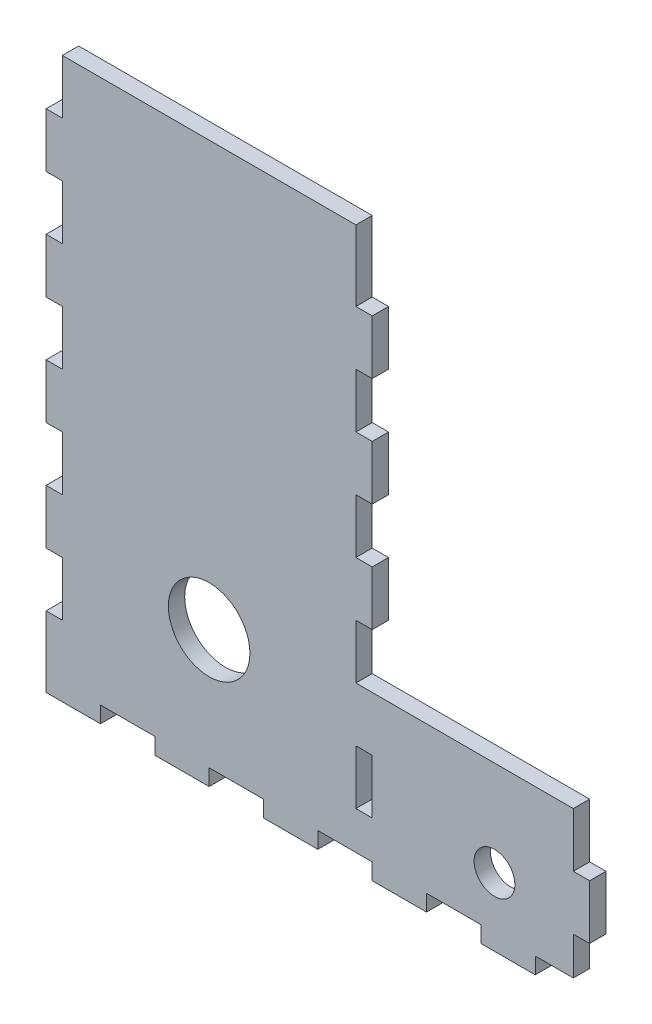
SolidWorks part; units mm, degrees
ref_plane "Front Plane" through (0, 0, 0) normal (0, 0, 1) x (1, 0, 0)
ref_plane "Top Plane" through (0, 0, 0) normal (0, 1, 0) x (1, 0, 0)
ref_plane "Right Plane" through (0, 0, 0) normal (1, 0, 0) x (0, 0, -1)
sketch "Sketch1" plane through (0, 0, 0) normal (0, 0, 1) x (1, 0, 0)
  line L1 (-17.3309, 199.4274) -> (102.6691, 199.4274)
  line L2 (-17.3309, 199.4274) -> (-17.3309, -6.5726)
  line L3 (-17.3309, -6.5726) -> (102.6691, -6.5726)
  line L4 (102.6691, 199.4274) -> (102.6691, 53.4274)
  line L5 (102.6691, -6.5726) -> (182.6691, -6.5726)
  line L7 (102.6691, 53.4274) -> (182.6691, 53.4274)
  line L8 (182.6691, -6.5726) -> (182.6691, 53.4274)
  dimension "D1" = 120
  dimension "D2" = 206
  dimension "D3" = 60
  dimension "D4" = 120
  dimension "D5" = 200
extrude "Boss-Extrude1" add sketch "Sketch1" along normal blind 6
sketch "Sketch2" plane through (0, 0, 6) normal (0, 0, 1) x (1, 0, 0)
  line L0 (-17.3309, -6.5726) -> (182.6691, -6.5726) construction
  line L1 (2.6691, -6.5726) -> (22.6691, -6.5726)
  line L2 (2.6691, -6.5726) -> (2.6691, -0.5726)
  line L3 (2.6691, -0.5726) -> (22.6691, -0.5726)
  line L4 (22.6691, -6.5726) -> (22.6691, -0.5726)
  line L5 (-17.3309, 199.4274) -> (-17.3309, -6.5726) construction
  dimension "D1" = 0
  dimension "D2" = 6
  dimension "D3" = 20
  dimension "D4" = 20
extrude "Cut-Extrude1" cut sketch "Sketch2" against normal through all
pattern_linear "LPattern1" count 5 spacing 40 along (1, 0, 0) of "Cut-Extrude1"
sketch "Sketch3" plane through (0, 0, 0) normal (0, 0, 1) x (1, 0, 0)
  line L5 (102.6691, 53.4274) -> (102.6691, 199.4274) construction
  line L6 (102.6691, 33.4274) -> (96.6691, 33.4274)
  line L7 (102.6691, 33.4274) -> (102.6691, 13.4274)
  line L8 (102.6691, 13.4274) -> (96.6691, 13.4274)
  line L9 (96.6691, 33.4274) -> (96.6691, 13.4274)
  line L10 (62.6691, -6.5726) -> (82.6691, -6.5726) construction
  dimension "D1" = 0
  dimension "D2" = 20
  dimension "D3" = 20
  dimension "D4" = 6
extrude "Cut-Extrude2" cut sketch "Sketch3" along normal through all
pattern_linear "LPattern2" count 5 spacing 40 along (0, 1, 0) of "Cut-Extrude2"
sketch "Sketch4" plane through (0, 0, 6) normal (0, 0, 1) x (1, 0, 0)
  line L1 (96.6691, 193.4274) -> (102.6691, 193.4274)
  line L2 (96.6691, 193.4274) -> (96.6691, 199.4274)
  line L3 (96.6691, 199.4274) -> (102.6691, 199.4274)
  line L4 (102.6691, 193.4274) -> (102.6691, 199.4274)
extrude "Cut-Extrude3" cut sketch "Sketch4" against normal blind 10
sketch "Sketch5" plane through (0, 0, 6) normal (0, 0, 1) x (1, 0, 0)
  line L1 (182.6691, 53.4274) -> (176.6691, 53.4274)
  line L2 (182.6691, 53.4274) -> (182.6691, 33.4274)
  line L3 (182.6691, 33.4274) -> (176.6691, 33.4274)
  line L4 (176.6691, 53.4274) -> (176.6691, 33.4274)
  dimension "D1" = 20
  dimension "D2" = 6
extrude "Cut-Extrude4" cut sketch "Sketch5" against normal blind 10
pattern_linear "LPattern3" count 2 spacing 40 along (0, -1, 0) of "Cut-Extrude4"
sketch "Sketch7" plane through (0, 0, 6) normal (0, 0, 1) x (1, 0, 0)
  line L1 (-17.3309, 199.4274) -> (-11.3309, 199.4274)
  line L2 (-17.3309, 199.4274) -> (-17.3309, 179.4274)
  line L3 (-17.3309, 179.4274) -> (-11.3309, 179.4274)
  line L4 (-11.3309, 199.4274) -> (-11.3309, 179.4274)
  dimension "D1" = 6
  dimension "D2" = 20
extrude "Cut-Extrude5" cut sketch "Sketch7" against normal blind 10
pattern_linear "LPattern4" count 5 spacing 40 along (0, -1, 0) of "Cut-Extrude5"
sketch "Sketch8" plane through (0, 0, 0) normal (0, 0, -1) x (-1, 0, 0)
  line L0 (17.3309, 59.4274) -> (17.3309, 39.4274) construction
  line L1 (-22.6691, -6.5726) -> (-42.6691, -6.5726) construction
  line L3 (-102.6691, 73.4274) -> (-102.6691, 93.4274) construction
  circle A0 centre (-42.6691, 43.4274) radius 15
  point P6 (0, 0)
  dimension "D1" = 30
  dimension "D2" = 60
  dimension "D3" = 50
  dimension "D4" = 60
extrude "Cut-Extrude6" cut sketch "Sketch8" against normal blind 10
sketch "Sketch9" plane through (0, 0, 0) normal (0, 0, -1) x (-1, 0, 0)
  line L0 (-142.6691, -6.5726) -> (-162.6691, -6.5726) construction
  line L1 (-182.6691, 13.4274) -> (-182.6691, 33.4274) construction
  circle A1 centre (-147.6691, 18.4274) radius 7.5
  dimension "D1" = 25
  dimension "D2" = 35
extrude "Cut-Extrude7" cut sketch "Sketch9" against normal through all
